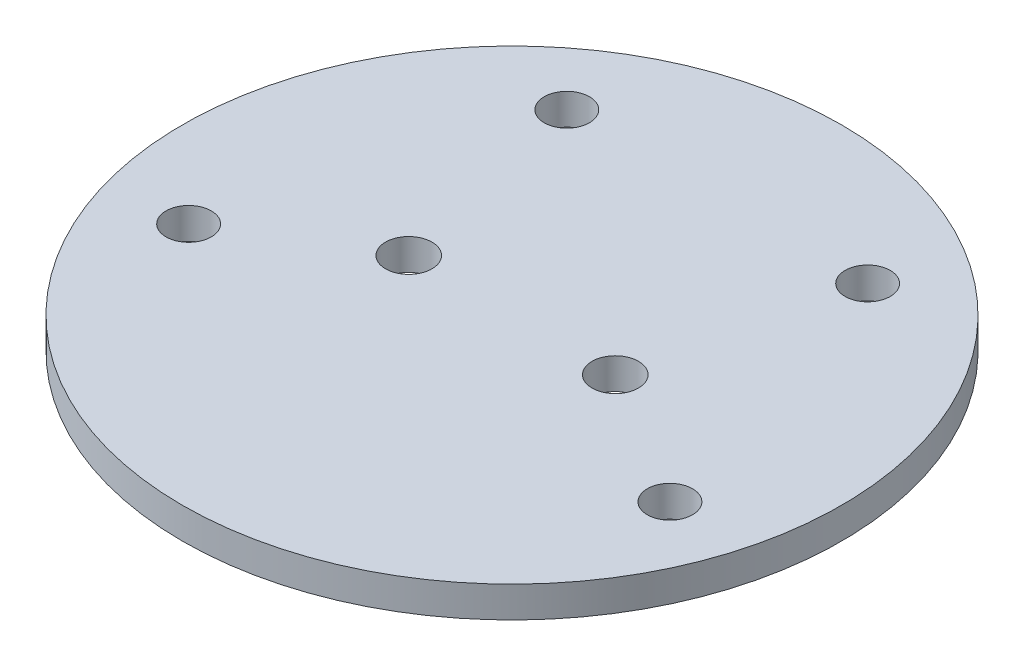
SolidWorks part; units mm, degrees
material "5052-H32"
ref_plane "Front Plane" through (0, 0, 0) normal (0, 0, 1) x (1, 0, 0)
ref_plane "Top Plane" through (0, 0, 0) normal (0, 1, 0) x (1, 0, 0)
ref_plane "Right Plane" through (0, 0, 0) normal (1, 0, 0) x (0, 0, -1)
sketch "Sketch1" plane through (0, 0, 0) normal (0, 1, 0) x (1, 0, 0)
  line L0 (0, 0) -> (-23.1297, 31.5565) construction
  line L1 (0, 0) -> (-41.7254, 0) construction
  line L2 (-37.0005, -12.7186) -> (0, 0) construction
  line L3 (0, -31.6103) -> (0, 47.1695) construction
  circle A0 centre (0, 0) radius 50.673
  circle A3 centre (-15.875, 0) radius 3.5687
  circle A4 centre (15.875, 0) radius 3.5687
  circle A5 centre (-37.0005, -12.7186) radius 3.475
  circle A8 centre (-23.1297, 31.5565) radius 3.475
  circle A9 centre (23.1297, 31.5565) radius 3.475
  circle A10 centre (37.0005, -12.7186) radius 3.475
  dimension "D1" = 101.346
  dimension "D2" = 6.95
  dimension "D3" = 6.95
  dimension "D10" = 7.1374
  dimension "D5" = 15.875
  dimension "D6" = 15.875
  dimension "D4" = 39.1254
  dimension "D7" = 53.76
  dimension "D8" = 39.1254
  dimension "D9" = 18.97
extrude "Boss-Extrude1" add sketch "Sketch1" along normal blind 4.7752
equation "\"allrockets_tube_ID\"= 3.85in"
equation "\"allrockets_tube_OD\"= 4.024in"
equation "\"hole\"= 6.35mm"
equation "\"back_plate_width\"= 28mm"
equation "\"card_spacing\"= 20mm"
equation "\"card_number\"= 5"
equation "\"ToDi\"= 0.05mm"
equation "\"card_diameter\"= 85.86mm"
equation "\"overlap\"= 6.6mm"
equation "\"card_length\"= 68mm"
equation "\"rack_hole_tol\"= 0.60mm"
equation "\"rack_front_width\"= 11.63mm"
equation "\"hole_b_d\"= 39.12541885mm"
equation "\"hole_b_a\"= 18.9721389deg"
equation "\"hole_u_d\"= 39.12541885mm"
equation "\"hole_u_a\"= 53.76090642deg"
equation "\"card_h\"= 61.73mm"
equation "\"sphinx_av\"= 50.292mm"
equation "\"tb_spacing\"= 40mm"
equation "\"D2@Sketch1\"=\"hole\"+\"rack_hole_tol\""
equation "\"D4@Sketch1\"=\"hole_u_d\""
equation "\"D7@Sketch1\"=\"hole_u_a\""
equation "\"D8@Sketch1\"=\"hole_b_d\""
equation "\"D9@Sketch1\"=\"hole_b_a\""
equation "\"D3@Sketch1\"=\"hole\"+\"rack_hole_tol\""
